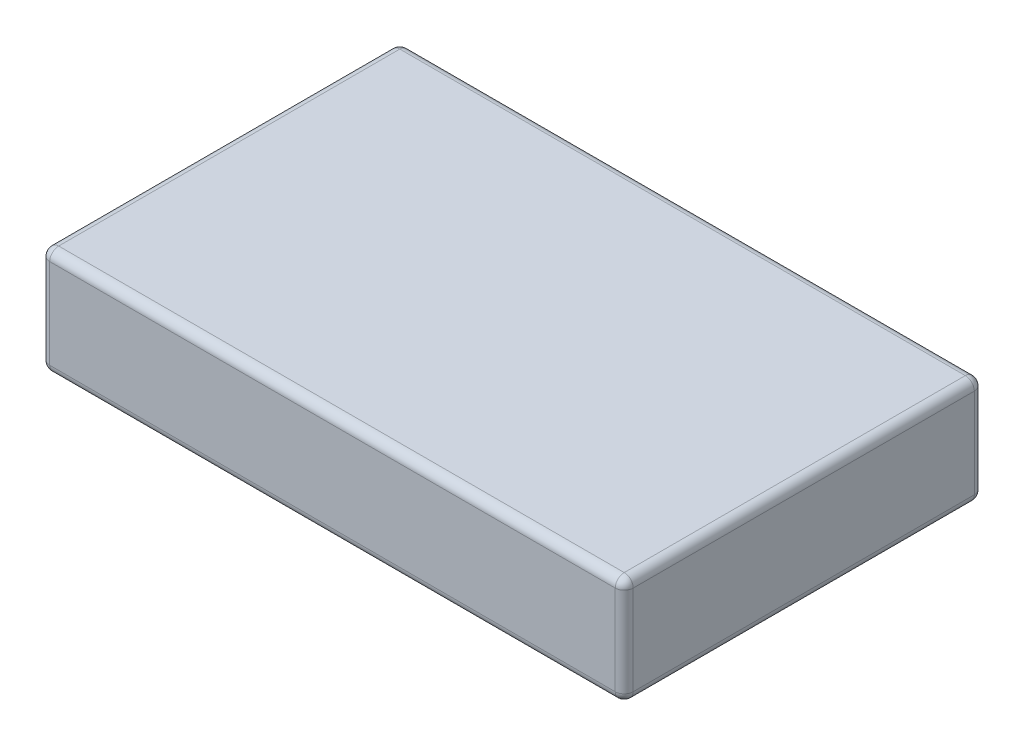
SolidWorks part; units mm, degrees
ref_plane "前视基准面" through (0, 0, 0) normal (0, 0, 1) x (1, 0, 0)
ref_plane "上视基准面" through (0, 0, 0) normal (0, 1, 0) x (1, 0, 0)
ref_plane "右视基准面" through (0, 0, 0) normal (1, 0, 0) x (0, 0, -1)
other "Configuration Table"
sketch "Sketch2" plane through (0, 0, 0) normal (0, 1, 0) x (1, 0, 0)
  line L1 (0, 0) -> (65, 0)
  line L2 (0, 0) -> (0, 40)
  line L3 (0, 40) -> (65, 40)
  line L4 (65, 0) -> (65, 40)
  dimension "D1" = 40
  dimension "D2" = 65
extrude "Boss-Extrude1" add sketch "Sketch2" along normal blind 12
fillet "Fillet1" radius 1 12 edges at (0, 0, -20) (0, 6, -40) (32.5, 0, -40) (65, 6, -40) (65, 0, -20) (32.5, 12, -40) (65, 12, -20) (0, 12, -20) (0, 6, 0) (32.5, 12, 0) (65, 6, 0) (32.5, 0, 0)
